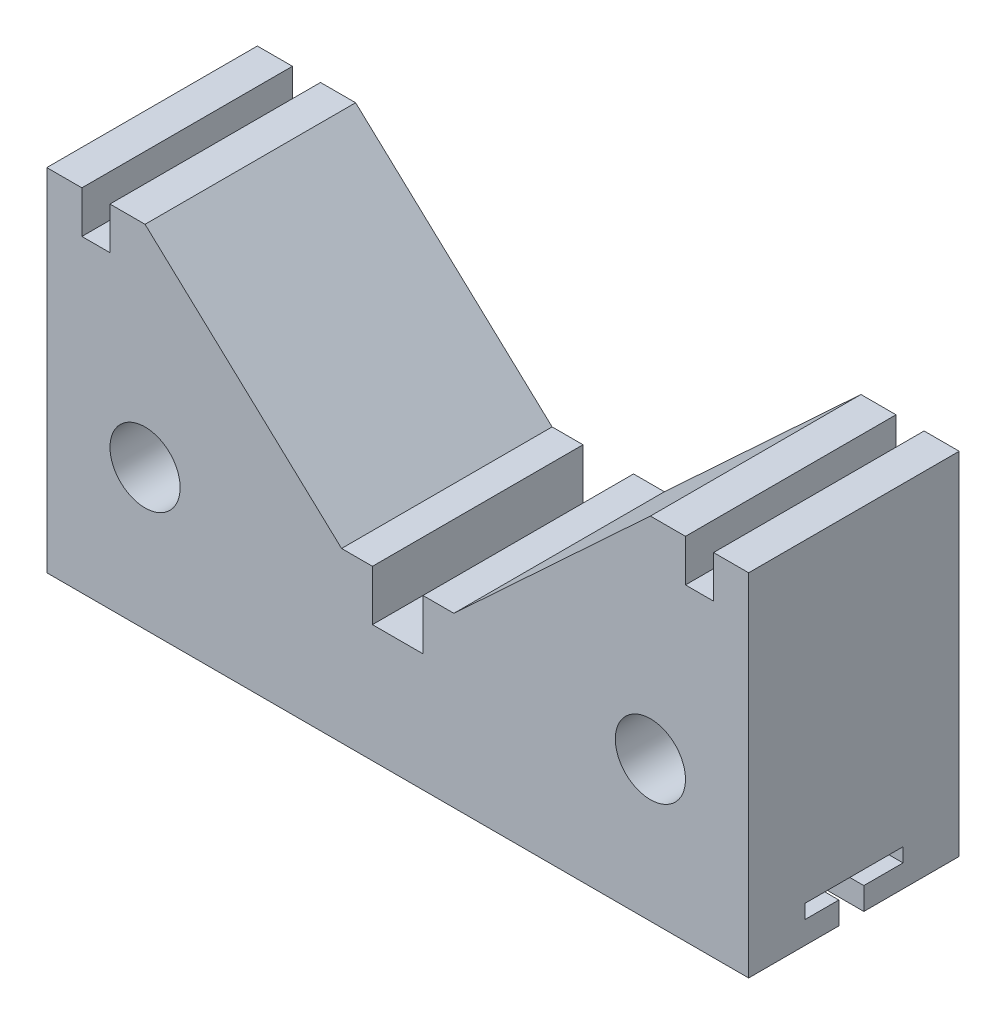
SolidWorks part; units mm, degrees
ref_plane "Front Plane" through (0, 0, 0) normal (0, 0, 1) x (1, 0, 0)
ref_plane "Top Plane" through (0, 0, 0) normal (0, 1, 0) x (1, 0, 0)
ref_plane "Right Plane" through (0, 0, 0) normal (1, 0, 0) x (0, 0, -1)
sketch "Sketch2" plane through (0, 0, 0) normal (0, 0, 1) x (1, 0, 0)
  line L0 (0, 151.3721) -> (0, -136.3597) construction
  line L1 (-242.6367, 0) -> (212.9784, 0) construction
  line L2 (-125, 0) -> (125, 0)
  line L3 (125, 0) -> (125, 125)
  line L4 (125, 125) -> (112.5, 125)
  line L5 (112.5, 125) -> (112.5, 110)
  line L6 (112.5, 110) -> (102.5, 110)
  line L7 (102.5, 110) -> (102.5, 125)
  line L8 (102.5, 125) -> (90, 125)
  line L9 (90, 125) -> (20, 60)
  line L10 (20, 60) -> (9, 60)
  line L11 (9, 60) -> (9, 42)
  line L12 (9, 42) -> (-9, 42)
  line L13 (-125, 0) -> (-125, 125)
  line L14 (-125, 125) -> (-112.5, 125)
  line L15 (-112.5, 125) -> (-112.5, 110)
  line L16 (-102.5, 110) -> (-102.5, 125)
  line L17 (-112.5, 110) -> (-102.5, 110)
  line L18 (-102.5, 125) -> (-90, 125)
  line L19 (-90, 125) -> (-20, 60)
  line L20 (-20, 60) -> (-9, 60)
  line L21 (-9, 60) -> (-9, 42)
  circle A0 centre (-90, 50) radius 12.5
  circle A1 centre (90, 50) radius 12.5
  point P19 (0, 0)
  point P21 (-125, 44.5065)
  point P33 (0, 42)
  dimension "D8" = 25
  dimension "D12" = 25
  dimension "D1" = 9
  dimension "D2" = 11
  dimension "D3" = 12.5
  dimension "D4" = 12.5
  dimension "D5" = 10
  dimension "D6" = 125
  dimension "D7" = 250
  dimension "D9" = 105
  dimension "D10" = 15
  dimension "D11" = 15
  dimension "D13" = 50
  dimension "D14" = 35
  dimension "D15" = 35
  dimension "D16" = 60
  dimension "D17" = 42
extrude "Boss-Extrude1" add sketch "Sketch2" along normal mid plane 75
sketch "Sketch3" plane through (125, 0, 0) normal (1, 0, 0) x (0, 0, -1)
  line L0 (0, 146.3095) -> (0, -68.7838) construction
  line L1 (-17.5, 13) -> (17.5, 13)
  line L2 (17.5, 13) -> (17.5, 8)
  line L3 (17.5, 8) -> (3.5301, 8)
  line L4 (3.5301, 8) -> (3.5301, 0)
  line L5 (-17.5, 13) -> (-17.5, 8)
  line L6 (-17.5, 8) -> (-5.3735, 8)
  line L7 (-5.3735, 8) -> (-5.3735, 0)
  line L8 (-37.5, 0) -> (37.5, 0) construction
  line L9 (-5.3735, 0) -> (3.5301, 0)
  point P6 (0, 13)
  dimension "D1" = 35
  dimension "D2" = 13
  dimension "D3" = 8
extrude "Cut-Extrude1" cut sketch "Sketch3" against normal blind 300
